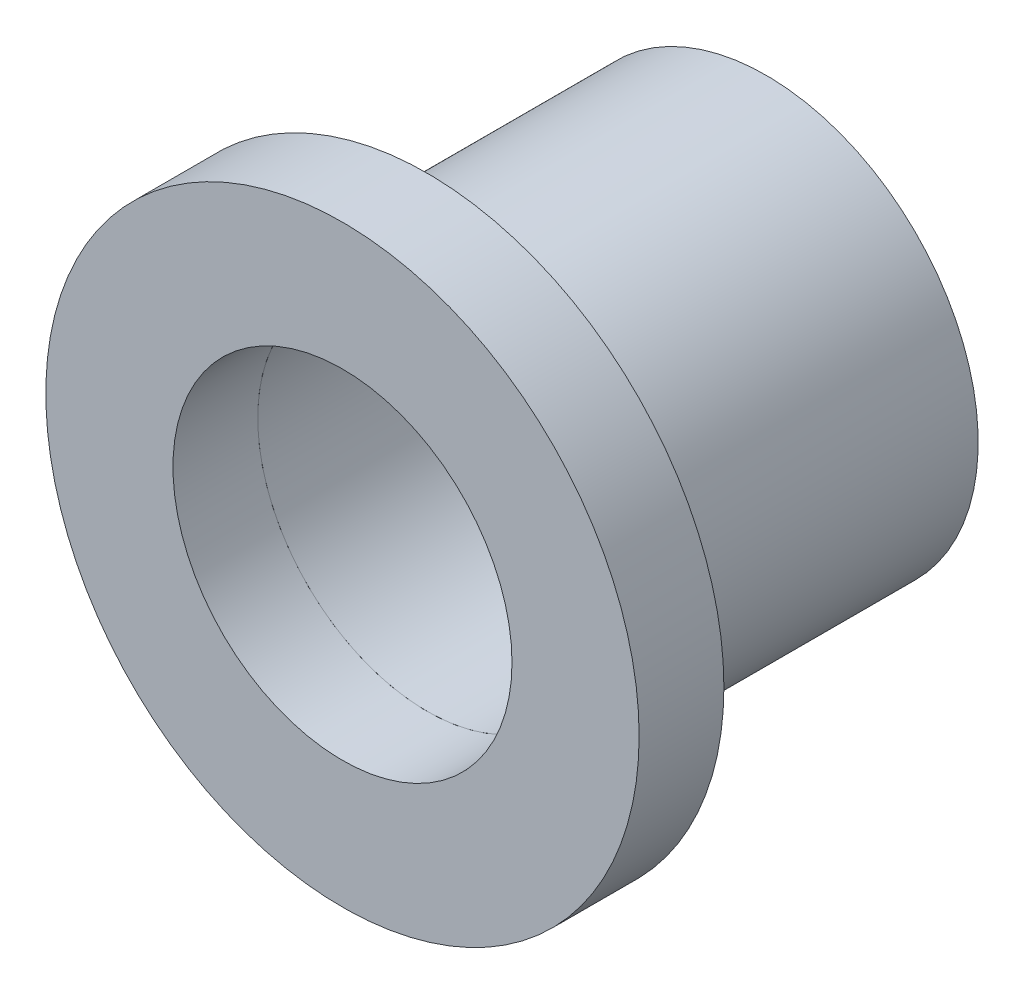
SolidWorks part; units mm, degrees
material "Commercial Bronze, UNS C22000 (90-10 Bronze)"
ref_plane "Front" through (0, 0, 0) normal (0, 0, 1) x (1, 0, 0)
ref_plane "Top" through (0, 0, 0) normal (0, 1, 0) x (1, 0, 0)
ref_plane "Right" through (0, 0, 0) normal (1, 0, 0) x (0, 0, -1)
sketch "Sketch1" plane through (0, 0, 0) normal (0, 0, 1) x (1, 0, 0)
  circle A0 centre (0, 0) radius 6.35
  circle A1 centre (0, 0) radius 11.1125
  dimension "D1" = 12.7
  dimension "D2" = 22.225
extrude "Boss-Extrude1" add sketch "Sketch1" along normal blind 3.175
sketch "Sketch2" plane through (0, 0, 0) normal (0, 0, -1) x (-1, 0, 0)
  circle A0 centre (0, 0) radius 6.35
  circle A1 centre (0, 0) radius 7.9375
  dimension "D1" = 15.875
  dimension "D2" = 12.7
extrude "Boss-Extrude2" add sketch "Sketch2" along normal blind 12.7 separate body
